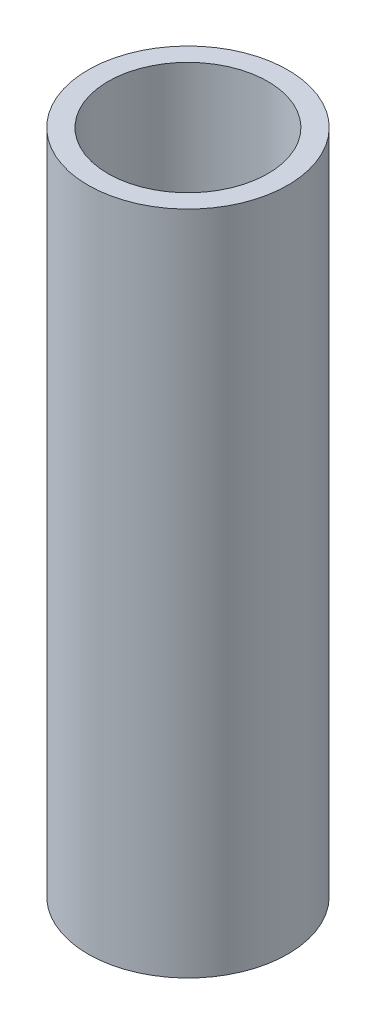
SolidWorks part; units mm, degrees
ref_plane "Front Plane" through (0, 0, 0) normal (0, 0, 1) x (1, 0, 0)
ref_plane "Top Plane" through (0, 0, 0) normal (0, 1, 0) x (1, 0, 0)
ref_plane "Right Plane" through (0, 0, 0) normal (1, 0, 0) x (0, 0, -1)
sketch "Sketch1" plane through (0, 0, 0) normal (0, 1, 0) x (1, 0, 0)
  circle A0 centre (0, 0) radius 15
  circle A1 centre (0, 0) radius 12
  dimension "D1" = 30
  dimension "D2" = 24
extrude "Boss-Extrude1" add sketch "Sketch1" along normal blind 100
